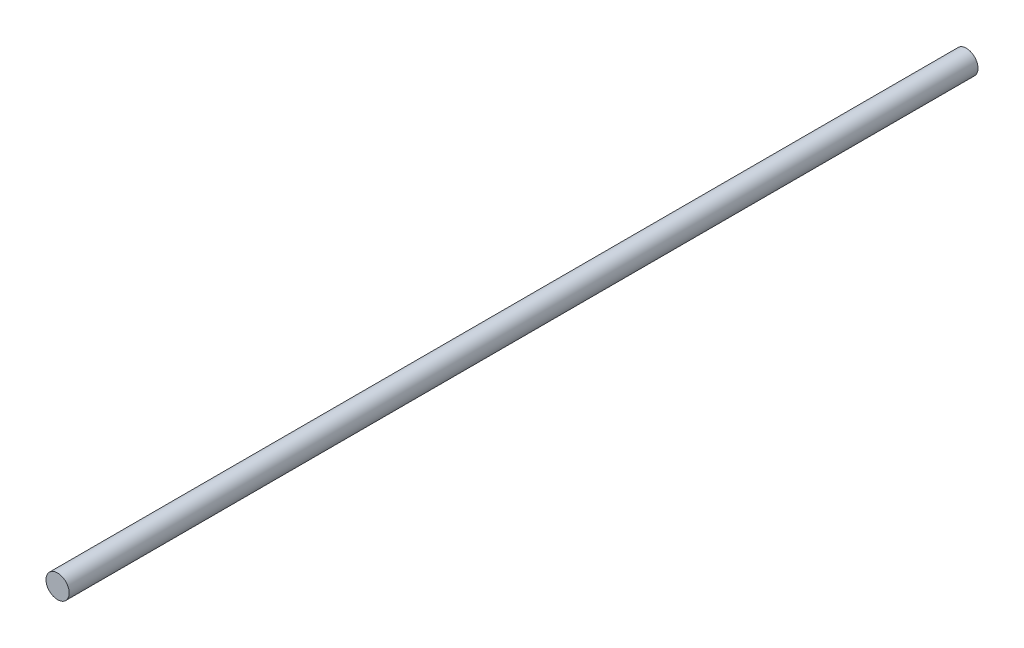
SolidWorks part; units mm, degrees
ref_plane "Front Plane" through (0, 0, 0) normal (0, 0, 1) x (1, 0, 0)
ref_plane "Top Plane" through (0, 0, 0) normal (0, 1, 0) x (1, 0, 0)
ref_plane "Right Plane" through (0, 0, 0) normal (1, 0, 0) x (0, 0, -1)
sketch "Sketch1" plane through (0, 0, 0) normal (0, 0, 1) x (1, 0, 0)
  circle A0 centre (0, 0) radius 3
  dimension "D1" = 6
extrude "Boss-Extrude1" add sketch "Sketch1" along normal blind 235
